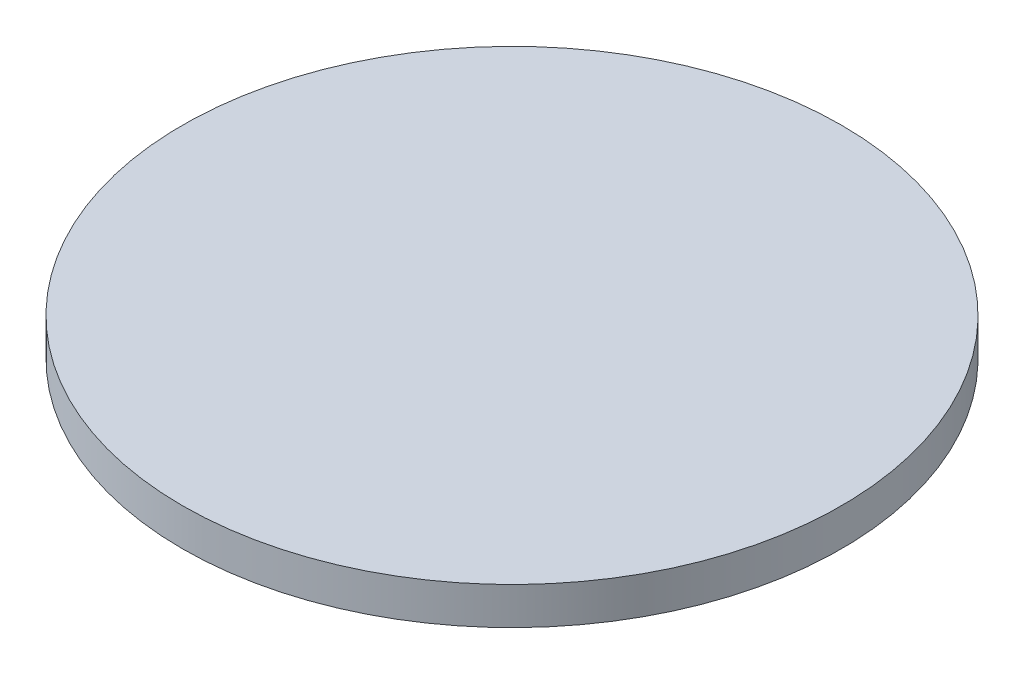
SolidWorks part; units mm, degrees
ref_plane "前视基准面" through (0, 0, 0) normal (0, 0, 1) x (1, 0, 0)
ref_plane "上视基准面" through (0, 0, 0) normal (0, 1, 0) x (1, 0, 0)
ref_plane "右视基准面" through (0, 0, 0) normal (1, 0, 0) x (0, 0, -1)
other "Configuration Table"
sketch "草图1" plane through (0, 0, 0) normal (0, 1, 0) x (1, 0, 0)
  circle A0 centre (0, 0) radius 15
  dimension "D1" = 30
extrude "凸台-拉伸1" add sketch "草图1" along normal blind 1.7
